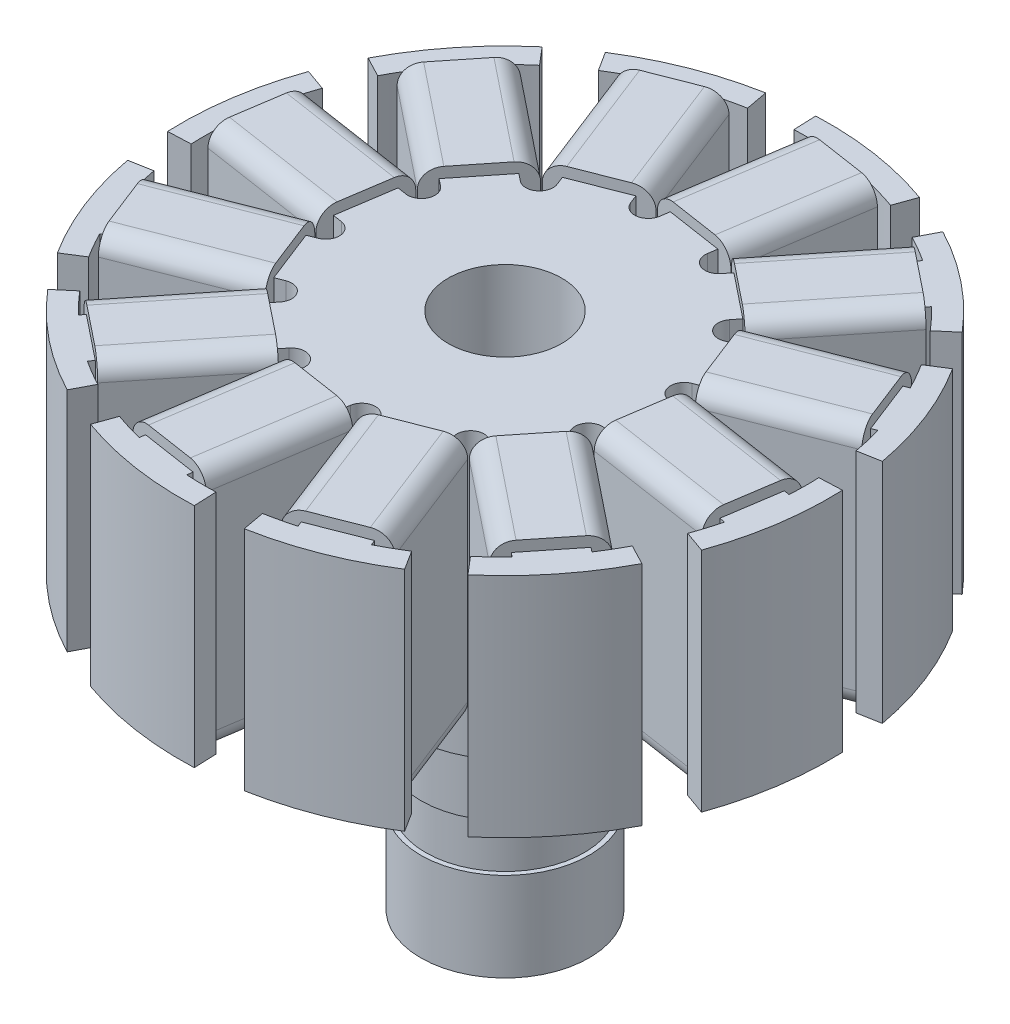
SolidWorks part; units mm, degrees
ref_plane "Front Plane" through (0, 0, 0) normal (0, 0, 1) x (1, 0, 0)
ref_plane "Top Plane" through (0, 0, 0) normal (0, 1, 0) x (1, 0, 0)
ref_plane "Right Plane" through (0, 0, 0) normal (1, 0, 0) x (0, 0, -1)
sketch "Sketch1" plane through (0, 0, 0) normal (0, 0, 1) x (1, 0, 0)
  line L0 (-4.45, 0) -> (0, 0)
  line L1 (-4.45, 0) -> (-4.45, 4.7)
  line L2 (-4.45, 4.7) -> (-4.2, 4.7)
  line L3 (-4.2, 4.7) -> (-4.2, 7.2)
  line L4 (-4.2, 7.2) -> (-4.45, 7.2)
  line L5 (-4.45, 7.2) -> (-4.45, 10.4)
  line L6 (-4.45, 10.4) -> (-5, 10.4)
  line L7 (-5, 28.4059) -> (-5, 29.9059) construction
  line L9 (-5, 10.4) -> (-5, 15.4059)
  line L10 (-5, 15.4059) -> (0, 15.4059)
  line L11 (0, 15.4059) -> (0, 0)
  line L12 (-5, 15.4059) -> (-5, 28.4059) construction
  dimension "D1" = 4.45
  dimension "D2" = 4.2
  dimension "D3" = 5
  dimension "D4" = 13
  dimension "D5" = 1.5
  dimension "D7" = 4.7
  dimension "D8" = 2.5
  dimension "D9" = 3.2
revolve "Revolve1" add sketch "Sketch1" angle 360 about L11
sketch "Sketch2" plane through (0, 15.4059, 0) normal (0, 1, 0) x (1, 0, 0)
  line L0 (-0.6574, 15.9364) -> (-0.7069, 17.1354)
  line L1 (5.3603, 15.0223) -> (5.7636, 16.1525)
  line L2 (0.9018, 15.9245) -> (-0.2386, 8.4172)
  line L3 (3.8678, 15.4739) -> (2.7274, 7.9667)
  line L4 (2.463, 16.214) -> (0, 0) construction
  line L5 (7.3989, 14.1301) -> (7.9555, 15.1932)
  line L6 (12.1533, 10.3295) -> (13.0677, 11.1067)
  line L7 (11.0866, 11.4669) -> (6.3454, 5.5357)
  line L8 (8.7433, 13.3401) -> (4.002, 7.4088)
  line L9 (13.4726, 8.5376) -> (14.4863, 9.1799)
  line L10 (15.6899, 2.869) -> (16.8703, 3.0848)
  line L11 (15.3347, 4.3873) -> (8.2631, 1.6213)
  line L12 (14.2419, 7.1812) -> (7.1703, 4.4152)
  line L13 (15.9364, 0.6574) -> (17.1354, 0.7069)
  line L14 (15.0223, -5.3603) -> (16.1525, -5.7636)
  line L15 (15.4739, -3.8678) -> (7.9667, -2.7274)
  line L16 (15.9245, -0.9018) -> (8.4172, 0.2386)
  line L17 (14.1301, -7.3989) -> (15.1932, -7.9555)
  line L18 (10.3295, -12.1533) -> (11.1067, -13.0677)
  line L19 (11.4669, -11.0866) -> (5.5357, -6.3454)
  line L20 (13.3401, -8.7433) -> (7.4088, -4.002)
  line L21 (8.5376, -13.4726) -> (9.1799, -14.4863)
  line L22 (2.869, -15.6899) -> (3.0848, -16.8703)
  line L23 (4.3873, -15.3347) -> (1.6213, -8.2631)
  line L24 (7.1812, -14.2419) -> (4.4152, -7.1703)
  line L25 (0.6574, -15.9364) -> (0.7069, -17.1354)
  line L26 (-5.3603, -15.0223) -> (-5.7636, -16.1525)
  line L27 (-3.8678, -15.4739) -> (-2.7274, -7.9667)
  line L28 (-0.9018, -15.9245) -> (0.2386, -8.4172)
  line L29 (-7.3989, -14.1301) -> (-7.9555, -15.1932)
  line L30 (-12.1533, -10.3295) -> (-13.0677, -11.1067)
  line L31 (-11.0866, -11.4669) -> (-6.3454, -5.5357)
  line L32 (-8.7433, -13.3401) -> (-4.002, -7.4088)
  line L33 (-13.4726, -8.5376) -> (-14.4863, -9.1799)
  line L34 (-15.6899, -2.869) -> (-16.8703, -3.0848)
  line L35 (-15.3347, -4.3873) -> (-8.2631, -1.6213)
  line L36 (-14.2419, -7.1812) -> (-7.1703, -4.4152)
  line L37 (-15.9364, -0.6574) -> (-17.1354, -0.7069)
  line L38 (-15.0223, 5.3603) -> (-16.1525, 5.7636)
  line L39 (-15.4739, 3.8678) -> (-7.9667, 2.7274)
  line L40 (-15.9245, 0.9018) -> (-8.4172, -0.2386)
  line L41 (-14.1301, 7.3989) -> (-15.1932, 7.9555)
  line L42 (-10.3295, 12.1533) -> (-11.1067, 13.0677)
  line L43 (-11.4669, 11.0866) -> (-5.5357, 6.3454)
  line L44 (-13.3401, 8.7433) -> (-7.4088, 4.002)
  line L45 (-8.5376, 13.4726) -> (-9.1799, 14.4863)
  line L46 (-2.869, 15.6899) -> (-3.0848, 16.8703)
  line L47 (-4.3873, 15.3347) -> (-1.6213, 8.2631)
  line L48 (-7.1812, 14.2419) -> (-4.4152, 7.1703)
  line L49 (35.1681, -11.0655) -> (35.1681, -12.5655) construction
  line L50 (32.5571, -11.0655) -> (40.3571, -11.0655) construction
  circle A0 centre (0, 0) radius 20.15 construction
  circle A1 centre (0, 0) radius 17.15 construction
  arc A2 (5.7636, 16.1525) -> (-0.7069, 17.1354) centre (0, 0) ccw
  arc A3 (5.3603, 15.0223) -> (3.8678, 15.4739) centre (0, 0) ccw
  arc A4 (0.9018, 15.9245) -> (-0.6574, 15.9364) centre (0, 0) ccw
  arc A5 (13.0677, 11.1067) -> (7.9555, 15.1932) centre (0, 0) ccw
  arc A6 (12.1533, 10.3295) -> (11.0866, 11.4669) centre (0, 0) ccw
  arc A7 (8.7433, 13.3401) -> (7.3989, 14.1301) centre (0, 0) ccw
  arc A8 (16.8703, 3.0848) -> (14.4863, 9.1799) centre (0, 0) ccw
  arc A9 (15.6899, 2.869) -> (15.3347, 4.3873) centre (0, 0) ccw
  arc A10 (14.2419, 7.1812) -> (13.4726, 8.5376) centre (0, 0) ccw
  arc A11 (16.1525, -5.7636) -> (17.1354, 0.7069) centre (0, 0) ccw
  arc A12 (15.0223, -5.3603) -> (15.4739, -3.8678) centre (0, 0) ccw
  arc A13 (15.9245, -0.9018) -> (15.9364, 0.6574) centre (0, 0) ccw
  arc A14 (11.1067, -13.0677) -> (15.1932, -7.9555) centre (0, 0) ccw
  arc A15 (10.3295, -12.1533) -> (11.4669, -11.0866) centre (0, 0) ccw
  arc A16 (13.3401, -8.7433) -> (14.1301, -7.3989) centre (0, 0) ccw
  arc A17 (3.0848, -16.8703) -> (9.1799, -14.4863) centre (0, 0) ccw
  arc A18 (2.869, -15.6899) -> (4.3873, -15.3347) centre (0, 0) ccw
  arc A19 (7.1812, -14.2419) -> (8.5376, -13.4726) centre (0, 0) ccw
  arc A20 (-5.7636, -16.1525) -> (0.7069, -17.1354) centre (0, 0) ccw
  arc A21 (-5.3603, -15.0223) -> (-3.8678, -15.4739) centre (0, 0) ccw
  arc A22 (-0.9018, -15.9245) -> (0.6574, -15.9364) centre (0, 0) ccw
  arc A23 (-13.0677, -11.1067) -> (-7.9555, -15.1932) centre (0, 0) ccw
  arc A24 (-12.1533, -10.3295) -> (-11.0866, -11.4669) centre (0, 0) ccw
  arc A25 (-8.7433, -13.3401) -> (-7.3989, -14.1301) centre (0, 0) ccw
  arc A26 (-16.8703, -3.0848) -> (-14.4863, -9.1799) centre (0, 0) ccw
  arc A27 (-15.6899, -2.869) -> (-15.3347, -4.3873) centre (0, 0) ccw
  arc A28 (-14.2419, -7.1812) -> (-13.4726, -8.5376) centre (0, 0) ccw
  arc A29 (-16.1525, 5.7636) -> (-17.1354, -0.7069) centre (0, 0) ccw
  arc A30 (-15.0223, 5.3603) -> (-15.4739, 3.8678) centre (0, 0) ccw
  arc A31 (-15.9245, 0.9018) -> (-15.9364, -0.6574) centre (0, 0) ccw
  arc A32 (-11.1067, 13.0677) -> (-15.1932, 7.9555) centre (0, 0) ccw
  arc A33 (-10.3295, 12.1533) -> (-11.4669, 11.0866) centre (0, 0) ccw
  arc A34 (-13.3401, 8.7433) -> (-14.1301, 7.3989) centre (0, 0) ccw
  arc A35 (-3.0848, 16.8703) -> (-9.1799, 14.4863) centre (0, 0) ccw
  arc A36 (-2.869, 15.6899) -> (-4.3873, 15.3347) centre (0, 0) ccw
  arc A37 (-7.1812, 14.2419) -> (-8.5376, 13.4726) centre (0, 0) ccw
  arc A38 (-1.6213, 8.2631) -> (-0.2386, 8.4172) centre (-0.9506, 8.5254) ccw
  arc A39 (2.7274, 7.9667) -> (4.002, 7.4088) centre (3.4395, 7.8585) ccw
  arc A40 (6.3454, 5.5357) -> (7.1703, 4.4152) centre (6.9079, 5.086) ccw
  arc A41 (8.2631, 1.6213) -> (8.4172, 0.2386) centre (8.5254, 0.9506) ccw
  arc A42 (7.9667, -2.7274) -> (7.4088, -4.002) centre (7.8585, -3.4395) ccw
  arc A43 (5.5357, -6.3454) -> (4.4152, -7.1703) centre (5.086, -6.9079) ccw
  arc A44 (1.6213, -8.2631) -> (0.2386, -8.4172) centre (0.9506, -8.5254) ccw
  arc A45 (-2.7274, -7.9667) -> (-4.002, -7.4088) centre (-3.4395, -7.8585) ccw
  arc A46 (-6.3454, -5.5357) -> (-7.1703, -4.4152) centre (-6.9079, -5.086) ccw
  arc A47 (-8.2631, -1.6213) -> (-8.4172, -0.2386) centre (-8.5254, -0.9506) ccw
  arc A48 (-7.9667, 2.7274) -> (-7.4088, 4.002) centre (-7.8585, 3.4395) ccw
  arc A49 (-5.5357, 6.3454) -> (-4.4152, 7.1703) centre (-5.086, 6.9079) ccw
  point P103 (0, 0)
  point P138 (0, 0)
  dimension "D1" = 40.3
  dimension "D2" = 3
  dimension "D3" = 1.2
  dimension "D4" = 22
  dimension "D5" = 3
  dimension "D8" = 1.5
  dimension "D9" = 7.8
  dimension "D6" = 12
  dimension "D7" = 12
extrude "Boss-Extrude1" add sketch "Sketch2" along normal blind 12
sketch "Sketch3" plane through (0, 27.4059, 0) normal (0, 1, 0) x (1, 0, 0)
  circle A0 centre (0, 0) radius 3
  dimension "D1" = 6
extrude "Cut-Extrude1" cut sketch "Sketch3" against normal through all
ref_plane "Plane1" through (-15.6992, 0, -2.3848) normal (0.9887, 0, 0.1502) x (0.1502, 0, -0.9887)
sketch "Sketch5" plane through (-15.6992, 0, -2.3848) normal (0.9887, 0, 0.1502) x (0.1502, 0, -0.9887)
  line L0 (6.4784, 27.4059) -> (5.4677, 27.4059)
  line L1 (3.0866, 27.4059) -> (1.5, 27.4059)
  line L2 (1.5, 27.4059) -> (-1.5, 27.4059)
  line L3 (-1.5, 27.4059) -> (-3.0866, 27.4059)
  line L4 (-5.4677, 27.4059) -> (-6.4784, 27.4059)
  line L5 (-5.4677, 27.4059) -> (-6.4784, 27.4059)
  line L6 (-1.5, 27.4059) -> (-3.0866, 27.4059)
  line L7 (1.5, 27.4059) -> (-1.5, 27.4059)
  line L8 (3.0866, 27.4059) -> (1.5, 27.4059)
  line L9 (6.4784, 27.4059) -> (5.4677, 27.4059)
  line L10 (1.5, 27.4059) -> (1.5, 15.4059)
  line L11 (1.5, 27.4059) -> (1.5, 15.4059)
  line L12 (-1.5, 27.4059) -> (-1.5, 15.4059)
  line L13 (-1.5, 27.4059) -> (-1.5, 15.4059)
  line L14 (6.4784, 15.4059) -> (5.4677, 15.4059)
  line L15 (3.0866, 15.4059) -> (1.5, 15.4059)
  line L16 (1.5, 15.4059) -> (-1.5, 15.4059)
  line L17 (-1.5, 15.4059) -> (-3.0866, 15.4059)
  line L18 (-5.4677, 15.4059) -> (-6.4784, 15.4059)
  line L19 (-5.4677, 15.4059) -> (-6.4784, 15.4059)
  line L20 (-1.5, 15.4059) -> (-3.0866, 15.4059)
  line L21 (1.5, 15.4059) -> (-1.5, 15.4059)
  line L22 (3.0866, 15.4059) -> (1.5, 15.4059)
  line L23 (6.4784, 15.4059) -> (5.4677, 15.4059)
  line L24 (0, 27.4059) -> (0, 15.4059) construction
  line L25 (1.3219, 14.8563) -> (-1.3219, 14.8563)
  line L26 (2.3219, 15.8563) -> (2.3219, 26.9555)
  line L27 (1.3219, 27.9555) -> (-1.3219, 27.9555)
  line L28 (-2.3219, 15.8563) -> (-2.3219, 26.9555)
  line L29 (2.3219, 14.8563) -> (-2.3219, 27.9555) construction
  line L30 (2.3219, 27.9555) -> (-2.3219, 14.8563) construction
  line L31 (1.5, 21.4059) -> (-1.5, 21.4059) construction
  arc A0 (1.3219, 14.8563) -> (2.3219, 15.8563) centre (1.3219, 15.8563) ccw
  arc A1 (-1.3219, 14.8563) -> (-2.3219, 15.8563) centre (-1.3219, 15.8563) cw
  arc A2 (-2.3219, 26.9555) -> (-1.3219, 27.9555) centre (-1.3219, 26.9555) cw
  arc A3 (1.3219, 27.9555) -> (2.3219, 26.9555) centre (1.3219, 26.9555) cw
  point P16 (0, 21.4059)
  dimension "D1" = 1
extrude "Boss-Extrude2" add sketch "Sketch5" along normal blind 6.8 from offset 0.3 contours L26 A3 L27 A2 L28 A1 L25 A0
pattern_circular "CirPattern1" count 12 over 360 about axis through (0, 0, 0) along (0, 1, 0) of "Boss-Extrude2"
